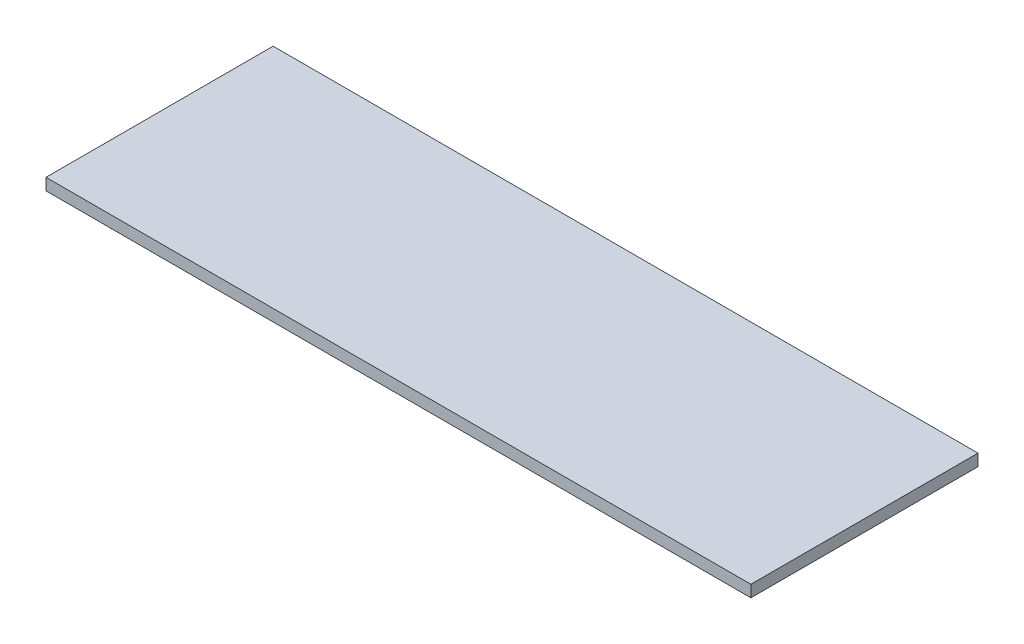
SolidWorks part; units mm, degrees
material "Pino"
ref_plane "Alzado" through (0, 0, 0) normal (0, 0, 1) x (1, 0, 0)
ref_plane "Planta" through (0, 0, 0) normal (0, 1, 0) x (1, 0, 0)
ref_plane "Vista lateral" through (0, 0, 0) normal (1, 0, 0) x (0, 0, -1)
sketch "Sketch1" plane through (0, 0, 0) normal (0, 1, 0) x (1, 0, 0)
  line L1 (-90, -29) -> (90, -29)
  line L2 (-90, -29) -> (-90, 29)
  line L3 (-90, 29) -> (90, 29)
  line L4 (90, -29) -> (90, 29)
  line L5 (-90, -29) -> (90, 29) construction
  line L6 (-90, 29) -> (90, -29) construction
  point P0 (0, 0)
  dimension "D1" = 180
  dimension "D2" = 58
extrude "Extrude1" add sketch "Sketch1" along normal blind 3
sketch "Sketch2" plane through (0, 3, 0) normal (0, 1, 0) x (1, 0, 0)
  circle A0 centre (0, -3) radius 11.25
  dimension "D1" = 22.5
  dimension "D2" = 3
extrude "Extrude2" [suppressed] cut sketch "Sketch2" against normal up to next
